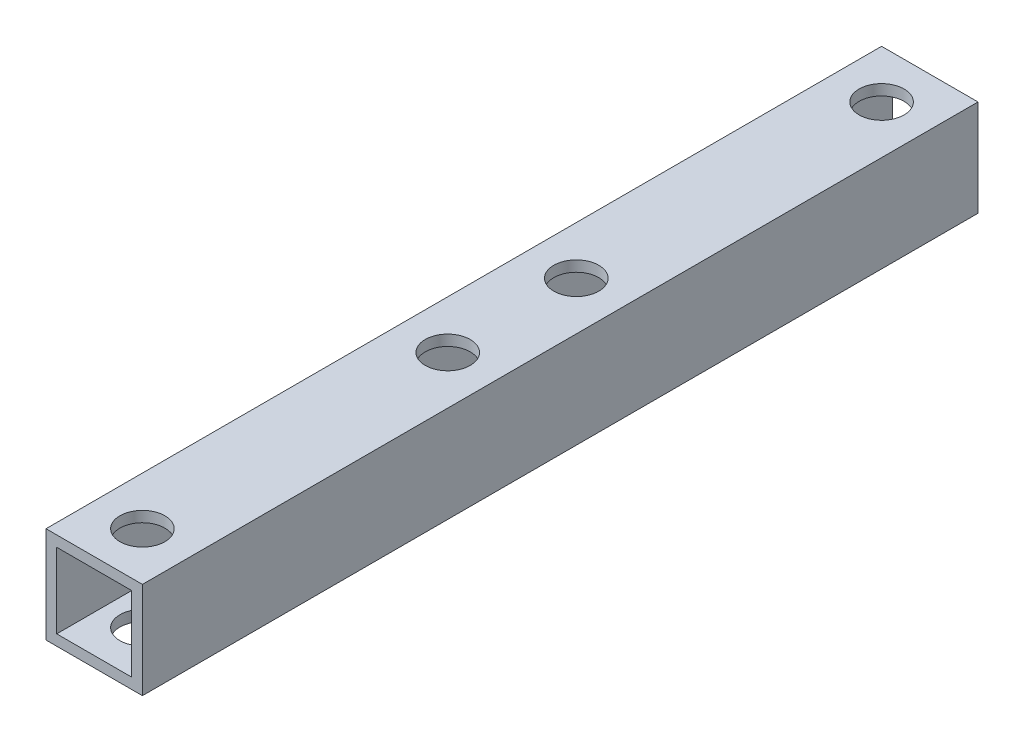
SolidWorks part; units mm, degrees
ref_plane "正面" through (0, 0, 0) normal (0, 0, 1) x (1, 0, 0)
ref_plane "平面" through (0, 0, 0) normal (0, 1, 0) x (1, 0, 0)
ref_plane "右側面" through (0, 0, 0) normal (1, 0, 0) x (0, 0, -1)
sketch "ｽｹｯﾁ1" plane through (0, 0, 0) normal (0, 0, 1) x (1, 0, 0)
  line L1 (-4.5, 4.5) -> (4.5, 4.5)
  line L2 (-4.5, 4.5) -> (-4.5, -4.5)
  line L3 (-4.5, -4.5) -> (4.5, -4.5)
  line L4 (4.5, 4.5) -> (4.5, -4.5)
  line L5 (-4.5, 4.5) -> (4.5, -4.5) construction
  line L6 (-4.5, -4.5) -> (4.5, 4.5) construction
  point P0 (0, 0)
  dimension "D1" = 9
  dimension "D2" = 9
extrude "ﾎﾞｽ - 押し出し1" add sketch "ｽｹｯﾁ1" along normal blind 78
sketch "ｽｹｯﾁ2" plane through (0, 0, 78) normal (0, 0, 1) x (1, 0, 0)
  line L1 (-3.5, 3.5) -> (3.5, 3.5)
  line L2 (-3.5, 3.5) -> (-3.5, -3.5)
  line L3 (-3.5, -3.5) -> (3.5, -3.5)
  line L4 (3.5, 3.5) -> (3.5, -3.5)
  line L5 (-3.5, 3.5) -> (3.5, -3.5) construction
  line L6 (-3.5, -3.5) -> (3.5, 3.5) construction
  point P0 (0, 0)
  dimension "D1" = 7
  dimension "D2" = 7
extrude "ｶｯﾄ - 押し出し1" cut sketch "ｽｹｯﾁ2" against normal blind 78
sketch "ｽｹｯﾁ3" plane through (0, 4.5, 0) normal (0, 1, 0) x (1, 0, 0)
  line L0 (0, 0) -> (0, -4.5)
  line L1 (0, -78) -> (0, -73.5)
  line L2 (4.5, -78) -> (-4.5, -78) construction
  circle A0 centre (0, -4.5) radius 2.1
  circle A1 centre (0, -73.5) radius 2.1
  dimension "D2" = 4.2
  dimension "D3" = 4.2
  dimension "D1" = 4.5
  dimension "D4" = 4.5
extrude "ｶｯﾄ - 押し出し2" cut sketch "ｽｹｯﾁ3" against normal blind 75
sketch "ｽｹｯﾁ4" plane through (0, 4.5, 0) normal (0, 1, 0) x (1, 0, 0)
  line L0 (0, 0) -> (0, -33)
  line L1 (0, -78) -> (0, -45)
  line L2 (4.5, -78) -> (-4.5, -78) construction
  circle A0 centre (0, -33) radius 2.1
  circle A1 centre (0, -45) radius 2.1
  dimension "D3" = 4.2
  dimension "D4" = 4.2
  dimension "D1" = 33
  dimension "D2" = 33
extrude "ｶｯﾄ - 押し出し3" cut sketch "ｽｹｯﾁ4" against normal blind 75
